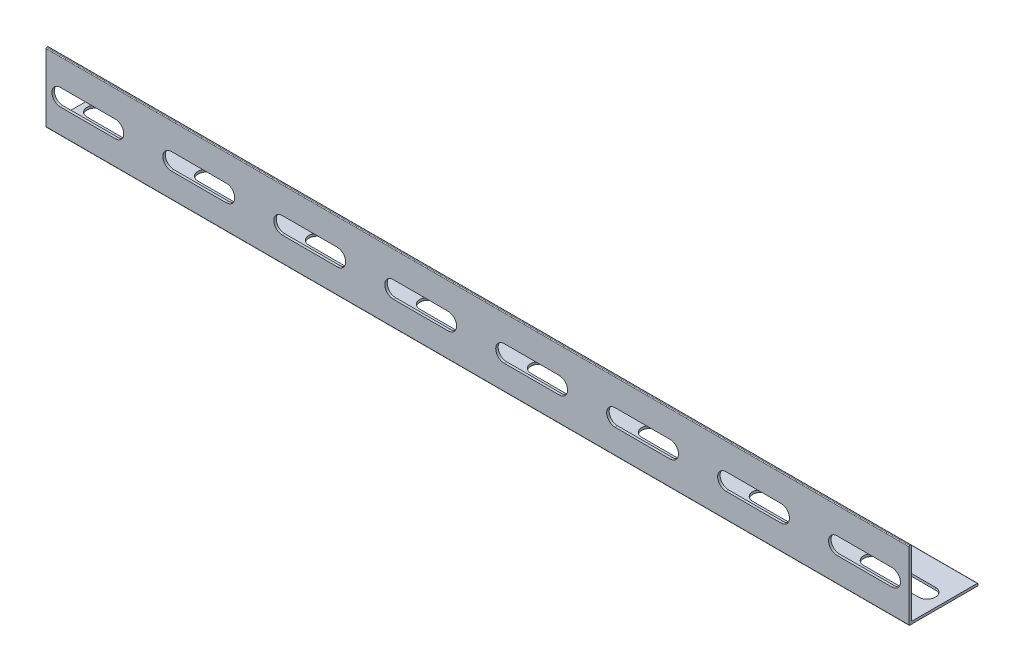
SolidWorks part; units mm, degrees
ref_plane "前视基准面" through (0, 0, 0) normal (0, 0, 1) x (1, 0, 0)
ref_plane "上视基准面" through (0, 0, 0) normal (0, 1, 0) x (1, 0, 0)
ref_plane "右视基准面" through (0, 0, 0) normal (1, 0, 0) x (0, 0, -1)
other "Configuration Table"
sketch "草图1" plane through (0, 0, 0) normal (1, 0, 0) x (0, 0, -1)
  line L1 (0, 0) -> (-5.4814, 0)
  line L2 (-4.7814, 1.3) -> (-4.7814, 27.7)
  line L3 (-5.0814, 28) -> (-5.4814, 28)
  line L4 (-5.7814, 0.3) -> (-5.7814, 27.7)
  line L5 (0, 0) -> (21.9186, 0)
  line L7 (-4.4814, 1) -> (21.9186, 1)
  line L8 (22.2186, 0.3) -> (22.2186, 0.7)
  arc A0 (-4.7814, 27.7) -> (-5.0814, 28) centre (-5.0814, 27.7) ccw
  arc A1 (-5.4814, 28) -> (-5.7814, 27.7) centre (-5.4814, 27.7) ccw
  arc A2 (21.9186, 0) -> (22.2186, 0.3) centre (21.9186, 0.3) ccw
  arc A3 (21.9186, 1) -> (22.2186, 0.7) centre (21.9186, 0.7) cw
  arc A4 (-4.7814, 1.3) -> (-4.4814, 1) centre (-4.4814, 1.3) ccw
  arc A5 (-5.4814, 0) -> (-5.7814, 0.3) centre (-5.4814, 0.3) cw
  point P10 (-4.7814, 28)
  point P13 (-5.7814, 28)
  point P16 (22.2186, 0)
  point P19 (22.2186, 1)
  point P24 (-5.7814, 0)
  dimension "D5" = 0.3
  dimension "D1" = 28
  dimension "D2" = 28
  dimension "D3" = 1
  dimension "D4" = 1
extrude "凸台-拉伸1" add sketch "草图1" along normal blind 350
sketch "草图2" plane through (0, 0, 5.7814) normal (0, 0, 1) x (1, 0, 0)
  line L0 (5.8347, 13.5438) -> (28.091, 13.5438) construction
  line L1 (5.8347, 16.9791) -> (28.091, 16.9791)
  line L2 (5.8347, 10.1084) -> (28.091, 10.1084)
  line L3 (50.8347, 13.5438) -> (73.091, 13.5438) construction
  line L4 (50.8347, 16.9791) -> (73.091, 16.9791)
  line L5 (50.8347, 10.1084) -> (73.091, 10.1084)
  line L6 (95.8347, 13.5438) -> (118.091, 13.5438) construction
  line L7 (95.8347, 16.9791) -> (118.091, 16.9791)
  line L8 (95.8347, 10.1084) -> (118.091, 10.1084)
  line L9 (140.8347, 13.5438) -> (163.091, 13.5438) construction
  line L10 (140.8347, 16.9791) -> (163.091, 16.9791)
  line L11 (140.8347, 10.1084) -> (163.091, 10.1084)
  line L12 (185.8347, 13.5438) -> (208.091, 13.5438) construction
  line L13 (185.8347, 16.9791) -> (208.091, 16.9791)
  line L14 (185.8347, 10.1084) -> (208.091, 10.1084)
  line L15 (230.8347, 13.5438) -> (253.091, 13.5438) construction
  line L16 (230.8347, 16.9791) -> (253.091, 16.9791)
  line L17 (230.8347, 10.1084) -> (253.091, 10.1084)
  line L18 (275.8347, 13.5438) -> (298.091, 13.5438) construction
  line L19 (275.8347, 16.9791) -> (298.091, 16.9791)
  line L20 (275.8347, 10.1084) -> (298.091, 10.1084)
  line L21 (320.8347, 13.5438) -> (343.091, 13.5438) construction
  line L22 (320.8347, 16.9791) -> (343.091, 16.9791)
  line L23 (320.8347, 10.1084) -> (343.091, 10.1084)
  arc A0 (5.8347, 16.9791) -> (5.8347, 10.1084) centre (5.8347, 13.5438) ccw
  arc A1 (28.091, 10.1084) -> (28.091, 16.9791) centre (28.091, 13.5438) ccw
  arc A2 (50.8347, 16.9791) -> (50.8347, 10.1084) centre (50.8347, 13.5438) ccw
  arc A3 (73.091, 10.1084) -> (73.091, 16.9791) centre (73.091, 13.5438) ccw
  arc A4 (95.8347, 16.9791) -> (95.8347, 10.1084) centre (95.8347, 13.5438) ccw
  arc A5 (118.091, 10.1084) -> (118.091, 16.9791) centre (118.091, 13.5438) ccw
  arc A6 (140.8347, 16.9791) -> (140.8347, 10.1084) centre (140.8347, 13.5438) ccw
  arc A7 (163.091, 10.1084) -> (163.091, 16.9791) centre (163.091, 13.5438) ccw
  arc A8 (185.8347, 16.9791) -> (185.8347, 10.1084) centre (185.8347, 13.5438) ccw
  arc A9 (208.091, 10.1084) -> (208.091, 16.9791) centre (208.091, 13.5438) ccw
  arc A10 (230.8347, 16.9791) -> (230.8347, 10.1084) centre (230.8347, 13.5438) ccw
  arc A11 (253.091, 10.1084) -> (253.091, 16.9791) centre (253.091, 13.5438) ccw
  arc A12 (275.8347, 16.9791) -> (275.8347, 10.1084) centre (275.8347, 13.5438) ccw
  arc A13 (298.091, 10.1084) -> (298.091, 16.9791) centre (298.091, 13.5438) ccw
  arc A14 (320.8347, 16.9791) -> (320.8347, 10.1084) centre (320.8347, 13.5438) ccw
  arc A15 (343.091, 10.1084) -> (343.091, 16.9791) centre (343.091, 13.5438) ccw
  point P2 (16.9628, 13.5438)
  point P7 (16.9628, 13.5438)
  point P10 (61.9628, 13.5438)
  point P18 (106.9628, 13.5438)
  point P25 (151.9628, 13.5438)
  point P32 (196.9628, 13.5438)
  point P39 (241.9628, 13.5438)
  point P46 (286.9628, 13.5438)
  point P53 (331.9628, 13.5438)
  dimension "D1" = 8
extrude "切除-拉伸1" cut sketch "草图2" against normal up to next
sketch "草图3" plane through (0, 1, 0) normal (0, 1, 0) x (1, 0, 0)
  line L0 (5.6565, 8.6331) -> (27.9128, 8.6331) construction
  line L1 (5.6565, 12.0685) -> (27.9128, 12.0685)
  line L2 (5.6565, 5.1978) -> (27.9128, 5.1978)
  line L3 (50.6565, 8.6331) -> (72.9128, 8.6331) construction
  line L4 (50.6565, 12.0685) -> (72.9128, 12.0685)
  line L5 (50.6565, 5.1978) -> (72.9128, 5.1978)
  line L6 (95.6565, 8.6331) -> (117.9128, 8.6331) construction
  line L7 (95.6565, 12.0685) -> (117.9128, 12.0685)
  line L8 (95.6565, 5.1978) -> (117.9128, 5.1978)
  line L9 (140.6565, 8.6331) -> (162.9128, 8.6331) construction
  line L10 (140.6565, 12.0685) -> (162.9128, 12.0685)
  line L11 (140.6565, 5.1978) -> (162.9128, 5.1978)
  line L12 (185.6565, 8.6331) -> (207.9128, 8.6331) construction
  line L13 (185.6565, 12.0685) -> (207.9128, 12.0685)
  line L14 (185.6565, 5.1978) -> (207.9128, 5.1978)
  line L15 (230.6565, 8.6331) -> (252.9128, 8.6331) construction
  line L16 (230.6565, 12.0685) -> (252.9128, 12.0685)
  line L17 (230.6565, 5.1978) -> (252.9128, 5.1978)
  line L18 (275.6565, 8.6331) -> (297.9128, 8.6331) construction
  line L19 (275.6565, 12.0685) -> (297.9128, 12.0685)
  line L20 (275.6565, 5.1978) -> (297.9128, 5.1978)
  line L21 (320.6565, 8.6331) -> (342.9128, 8.6331) construction
  line L22 (320.6565, 12.0685) -> (342.9128, 12.0685)
  line L23 (320.6565, 5.1978) -> (342.9128, 5.1978)
  arc A0 (5.6565, 12.0685) -> (5.6565, 5.1978) centre (5.6565, 8.6331) ccw
  arc A1 (27.9128, 5.1978) -> (27.9128, 12.0685) centre (27.9128, 8.6331) ccw
  arc A2 (50.6565, 12.0685) -> (50.6565, 5.1978) centre (50.6565, 8.6331) ccw
  arc A3 (72.9128, 5.1978) -> (72.9128, 12.0685) centre (72.9128, 8.6331) ccw
  arc A4 (95.6565, 12.0685) -> (95.6565, 5.1978) centre (95.6565, 8.6331) ccw
  arc A5 (117.9128, 5.1978) -> (117.9128, 12.0685) centre (117.9128, 8.6331) ccw
  arc A6 (140.6565, 12.0685) -> (140.6565, 5.1978) centre (140.6565, 8.6331) ccw
  arc A7 (162.9128, 5.1978) -> (162.9128, 12.0685) centre (162.9128, 8.6331) ccw
  arc A8 (185.6565, 12.0685) -> (185.6565, 5.1978) centre (185.6565, 8.6331) ccw
  arc A9 (207.9128, 5.1978) -> (207.9128, 12.0685) centre (207.9128, 8.6331) ccw
  arc A10 (230.6565, 12.0685) -> (230.6565, 5.1978) centre (230.6565, 8.6331) ccw
  arc A11 (252.9128, 5.1978) -> (252.9128, 12.0685) centre (252.9128, 8.6331) ccw
  arc A12 (275.6565, 12.0685) -> (275.6565, 5.1978) centre (275.6565, 8.6331) ccw
  arc A13 (297.9128, 5.1978) -> (297.9128, 12.0685) centre (297.9128, 8.6331) ccw
  arc A14 (320.6565, 12.0685) -> (320.6565, 5.1978) centre (320.6565, 8.6331) ccw
  arc A15 (342.9128, 5.1978) -> (342.9128, 12.0685) centre (342.9128, 8.6331) ccw
  point P2 (16.7847, 8.6331)
  point P10 (61.7847, 8.6331)
  point P18 (106.7847, 8.6331)
  point P25 (151.7847, 8.6331)
  point P32 (196.7847, 8.6331)
  point P39 (241.7847, 8.6331)
  point P46 (286.7847, 8.6331)
  point P53 (331.7847, 8.6331)
  dimension "D1" = 8
extrude "切除-拉伸2" cut sketch "草图3" against normal up to next
